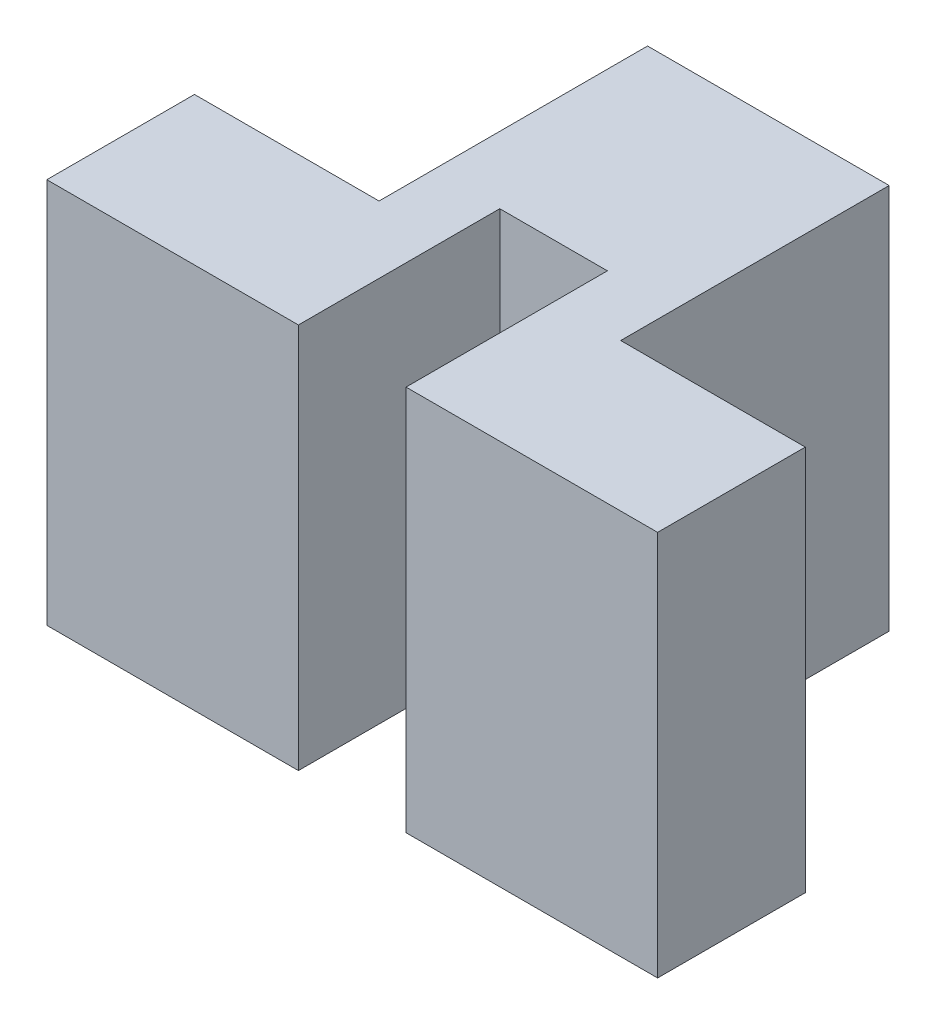
SolidWorks part; units mm, degrees
ref_plane "Front Plane" through (0, 0, 0) normal (0, 0, 1) x (1, 0, 0)
ref_plane "Top Plane" through (0, 0, 0) normal (0, 1, 0) x (1, 0, 0)
ref_plane "Right Plane" through (0, 0, 0) normal (1, 0, 0) x (0, 0, -1)
sketch "Sketch1" plane through (0, 0, 0) normal (0, 0, 1) x (1, 0, 0)
  line L0 (-8.75, 8.5) -> (-8.75, 11.5) construction
  line L1 (-8.5, 8.5) -> (-17.6, 8.5)
  line L2 (-8.5, 8.5) -> (-8.5, 14.25)
  line L3 (-8.5, 14.25) -> (-17.6, 14.25)
  line L4 (-17.6, 8.5) -> (-17.6, 14.25)
  line L6 (-17.85, 11.5) -> (-17.85, 8.5) construction
  line L7 (-17.85, 8.5) -> (-15.25, 8.5) construction
  line L8 (-15.25, 14.5) -> (-17.85, 14.5) construction
  dimension "D1" = 0.25
  dimension "D2" = 0.25
  dimension "D3" = 0.25
extrude "Boss-Extrude1" add sketch "Sketch1" along normal blind 2.2
sketch "Sketch3" plane through (0, 0, 0) normal (0, 0, -1) x (-1, 0, 0)
  line L0 (8.5, 14.25) -> (17.6, 14.25) construction
  line L1 (14.85, 14.25) -> (11.25, 14.25)
  line L2 (14.85, 14.25) -> (14.85, 8.5)
  line L3 (14.85, 8.5) -> (11.25, 8.5)
  line L4 (11.25, 14.25) -> (11.25, 8.5)
  line L5 (17.6, 8.5) -> (8.5, 8.5) construction
  line L8 (8.5, 8.5) -> (8.5, 14.25) construction
  line L9 (17.6, 14.25) -> (17.6, 8.5) construction
  dimension "D1" = 2.75
  dimension "D2" = 2.75
extrude "Boss-Extrude2" add sketch "Sketch3" along normal blind 4
sketch "Sketch2" plane through (0, 0, 2.2) normal (0, 0, 1) x (1, 0, 0)
  line L0 (-8.5, 8.5) -> (-8.5, 14.25) construction
  line L1 (-13.8517, 3.875) -> (-12.2483, 3.875)
  line L2 (-13.8517, 3.875) -> (-13.8517, 18.875)
  line L3 (-13.8517, 18.875) -> (-12.2483, 18.875)
  line L4 (-12.2483, 3.875) -> (-12.2483, 18.875)
  line L5 (-8.5, 14.25) -> (-17.6, 14.25) construction
  point P4 (-12.2483, 11.375)
  point P7 (-8.5, 11.375)
  point P8 (-13.05, 18.875)
  point P11 (-13.05, 14.25)
  dimension "D1" = 15
  dimension "D2" = 1.6033
extrude "Cut-Extrude1" cut sketch "Sketch2" against normal blind 3
